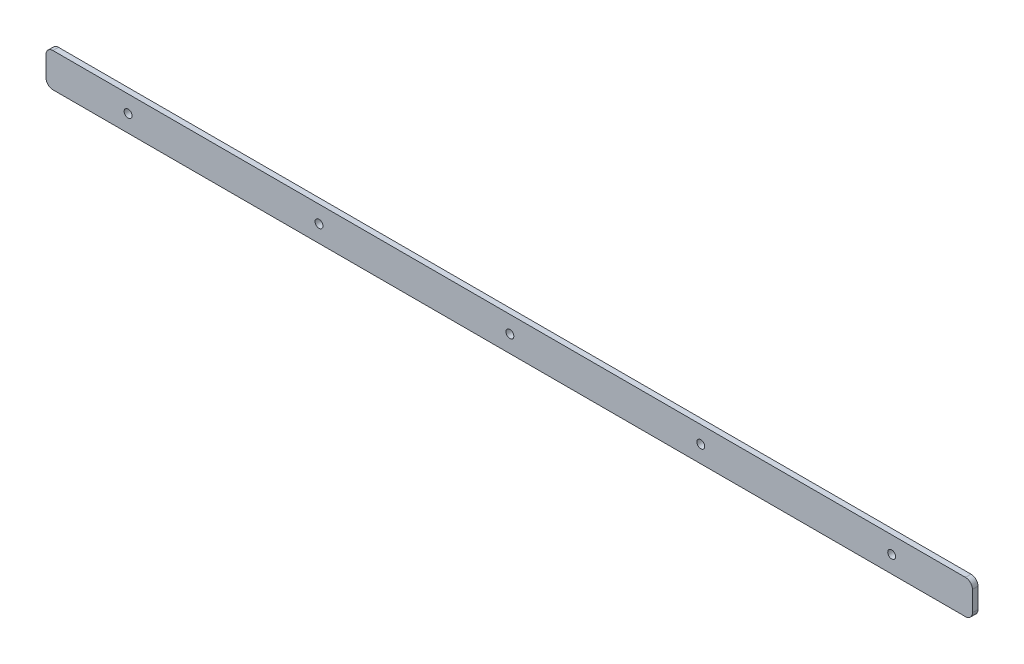
SolidWorks part; units mm, degrees
material "Acrylic (Medium-high impact)"
ref_plane "Front Plane" through (0, 0, 0) normal (0, 0, 1) x (1, 0, 0)
ref_plane "Top Plane" through (0, 0, 0) normal (0, 1, 0) x (1, 0, 0)
ref_plane "Right Plane" through (0, 0, 0) normal (1, 0, 0) x (0, 0, -1)
sketch "Sketch1" plane through (0, 0, 0) normal (0, 0, 1) x (1, 0, 0)
  line L1 (0, 0) -> (528.828, 0)
  line L2 (0, 0) -> (0, 19.431)
  line L3 (0, 19.431) -> (528.828, 19.431)
  line L4 (528.828, 0) -> (528.828, 19.431)
  dimension "D1" = 528.828
  dimension "D2" = 19.431
extrude "Boss-Extrude1" add sketch "Sketch1" along normal blind 3.175
hole_wizard "#8 Clearance Hole1" positions "Sketch2" profile "Sketch3" hole size "#8" standard "ANSI Inch" end condition through all
sketch "Sketch2" plane through (0, 0, 3.175) normal (0, 0, 1) x (1, 0, 0)
  line L0 (0, 9.7155) -> (528.828, 9.7155) construction
  line L1 (0, 19.431) -> (0, 0) construction
  line L2 (528.828, 0) -> (528.828, 19.431) construction
  line L3 (264.414, 19.431) -> (264.414, 0) construction
  line L4 (528.828, 19.431) -> (0, 19.431) construction
  line L5 (0, 0) -> (528.828, 0) construction
  point P0 (46.863, 9.7155)
  dimension "D1" = 217.551
sketch "Sketch3" plane through (46.863, 9.7155, 3.175) normal (1, 0, 0) x (0, -1, 0)
  line L0 (0, 0) -> (0, 3.175)
  line L1 (0, 3.175) -> (2.2479, 3.175)
  line L2 (2.2479, 3.175) -> (2.2479, 0)
  line L5 (2.2479, 0) -> (0, 0)
  line L11 (0, -6.35) -> (0, 107.95) construction
  dimension "Thru Hole Dia." = 4.4958
  dimension "Thru Hole Depth" = 3.175
fillet "Fillet1" radius 3.9688 4 edges at (0, 19.431, 1.5875) (0, 0, 1.5875) (528.828, 0, 1.5875) (528.828, 19.431, 1.5875)
pattern_linear "LPattern1" count 5 spacing 108.966 along (1, 0, 0) of "#8 Clearance Hole1"
equation "\"Height\"= 32in"
equation "\"Width\"= 23in"
equation "\"Depth\"= 20in"
equation "\"Plexi\"= .121in"
equation "\"EBWidth\" = 9in"
equation "\"ComponentMountDia\"=0.1770"
equation "\"MagnetThickness\"= 0.125in"
equation "\"MagnetDiameter\"= 12mm"
equation "\"DoorPlexi\" = \"Plexi\""
equation "\"ShelfThickness\" = .1250in"
equation "\"BasePlateThickness\" = 0.5in"
equation "\"BasePlateWidth\" = \"Width\"+\"EBWidth\"-2*\"Plexi\""
equation "\"BasePlateDepth\" = \"TopBarDepth\"+2*\"CornerCube\""
equation "\"Boxsize\" = .75in"
equation "\"BoxsizeHalf\" = \"Boxsize\"/2"
equation "\"Boxinner\" = .625in"
equation "\"CornerCube\" = 0.75in"
equation "\"FingerLength\" = 1.125in"
equation "\"FingerWidth\" = .625in"
equation "\"Cutwidth\"= .016in"
equation "\"Earsize\"= 1in + \"Cutwidth\" /2"
equation "\"Slotsize\" = 1in - \"CutWidth\" / 2"
equation "\"InnerWidth\" = \"Width\" - 2* \"Plexi\""
equation "\"InnerHeight\" = \"Height\" -2 * \"Plexi\""
equation "\"InnerDepth\" = \"Depth\" - 2*\"Plexi\""
equation "\"FrontDoorGap\" = .1in"
equation "\"TopDepth\" = \"Depth\"-\"DoorPlexi\"-\"FrontDoorGap\""
equation "\"TopBarDepth\" = \"Depth\"-\"DoorPlexi\"-\"Plexi\"-2*\"MagnetThickness\"-2*\"CornerCube\""
equation "\"RearNumHoles\" = 4"
equation "\"RearHolesBorder\" = 2.25"
equation "\"RearHoleSpacing\" = (\"Width\" - 2*\"RearHolesBorder\") / (\"RearNumHoles\"-1)"
equation "\"RearBarLength\" = (\"InnerWidth\"-2*\"CornerCube\")"
equation "\"RearTopNumHoles\" = 4"
equation "\"RearTopHolesBorder\" = 3.1"
equation "\"RearTopHolesSpacing\" = (\"Width\" - 2*\"RearTopHolesBorder\") / (\"RearTopNumHoles\"-1)"
equation "\"SideTopNumHoles\" = 4"
equation "\"SideTopHoleOffset\"=\"CornerCube\"+\"FingerLength\"+\"Plexi\"+.5"
equation "\"SideTopHoleSpacing\" = (\"TopBarDepth\"-2*\"SideTopHoleOffset\") / (\"SideTopNumHoles\"-1)"
equation "\"SideHorizNumHoles\" = 4"
equation "\"SideHorizHoleBorder\" = 1.50"
equation "\"SideHorizHoleSpacing\" = (\"TopBarDepth\"-2*\"SideHorizHoleBorder\") / (\"SideHorizNumHoles\"-1)"
equation "\"SideVertBarLength\"=\"Height\"-\"BasePlateThickness\"-2*\"CornerCube\"-\"Plexi\""
equation "\"SideVertNumHoles\" = 4"
equation "\"SideVertHolesBorder\" = \"CornerCube\"+\"FingerLength\"+1.50"
equation "\"SideVertHoleSpacing\" = (\"SideVertBarLength\" - 2*(\"SideVertHolesBorder\"-\"Plexi\"-\"CornerCube\")) / (\"SideVertNumHoles\"-1)"
equation "\"RearSideVertNumHoles\" = 4"
equation "\"RearSideVertHolesBorder\" = 2.4"
equation "\"RearSideVertHoleSpacing\" = (\"SideVertBarLength\" - 2*(\"RearSideVertHolesBorder\"-\"Plexi\"-\"CornerCube\")) / (\"RearSideVertNumHoles\"-1)"
equation "\"Rivet3_16Dia\" = .191in"
equation "\"RivetDia\" = .228in"
equation "\"BinderPostDia\" = .228in"
equation "\"SlotDepth\" = \"Plexi\" + 0.75in + .005in"
equation "\"SideSlotWidth\"   = \"Plexi\"+.005in"
equation "\"SidePanelVertSpacing\" = (\"Height\"-2*(1.75-\"Plexi\")) / 5"
equation "\"BottomPanelSideHoleSpacing\" = (\"InnerDepth\"-2*(1.75-\"Plexi\")) / 4"
equation "\"CoolerDepth\" = 12in"
equation "\"ShelfGap\" = 0.5in"
equation "\"ShelfDepth\" = \"TopBarDepth\"+\"CornerCube\"-\"CoolerDepth\""
equation "\"ShelfBarDepth\"=\"ShelfDepth\"-2*\"CornerCube\""
equation "\"ShelfWidth\" = \"EBWidth\"-\"ShelfGap\""
equation "\"ShelfBarWidth\" = \"EBWidth\"-\"Boxsize\""
equation "\"ShelfBarWidthShort\" = \"ShelfBarWidth\"-\"Boxsize\"-\"ShelfGap\""
equation "\"ShelfHeight1\" = 13in"
equation "\"ShelfHeight2\" = 24in"
equation "\"IntakeWidth\"=4in"
equation "\"IntakeHeight\"=2in"
equation "\"ExhaustWidth\"=4in"
equation "\"ExhaustHeight\"=2in"
equation "\"VentSpacing\"=7in"
equation "\"VentVertLocation\"=12.75in"
equation "\"AngleBracketLengthShort\"=.625in"
equation "\"AngleBracketLengthLong\"=1in"
equation "\"AngleBracketWidth\"=.5in"
equation "\"AngleBracketThickness\"=.125in"
equation "\"AngleBracketHolePosShort\"=.358in"
equation "\"AngleBracketHolePosLong\"=.7in"
equation "\"AngleBracketHoleDia\"=\"Rivet3_16Dia\""
equation "\"ShelfBarAngleHole\"=\"ShelfGap\"+\"Boxsize\"+\"AngleBracketHolePosShort\""
equation "\"PSBracketThickness\" = .0641in"
equation "\"EBForwardMountOffset\" = 4.0in"
equation "\"EBForwardMount\" = 2*\"Boxsize\"+\"CoolerDepth\"+\"EBForwardMountOffset\""
equation "\"EBRearwardMountOffset\" = 1.5in"
equation "\"EBRearwardMount\"= \"Boxsize\"+\"EBRearwardMountOffset\""
equation "\"MagSealWidth\" = \"InnerWidth\""
equation "\"MagSealHeight\" = \"Height\"-\"BasePlateThickness\"-\"Plexi\""
equation "\"MagWidth\" = .500in"
equation "\"SiliconeSealOD\" = .3125in"
equation "\"SiliconeSealID\" = .1875in"
equation "\"SiliconeSealWidth\" = \"MagSealWidth\" - 2*\"MagWidth\"-\"SiliconeSealOD\""
equation "\"SiliconeSealHeigth\" = \"MagSealHeight\" - 2*\"MagWidth\"-\"SiliconeSealOD\""
equation "\"HooknLoopThick\" = .085in"
equation "\"HooknLoopWidth\" = 0.75in"
equation "\"HooknLoopHeigth\" = 0.75in"
equation "\"D3@LPattern1\"=1.43*3"
